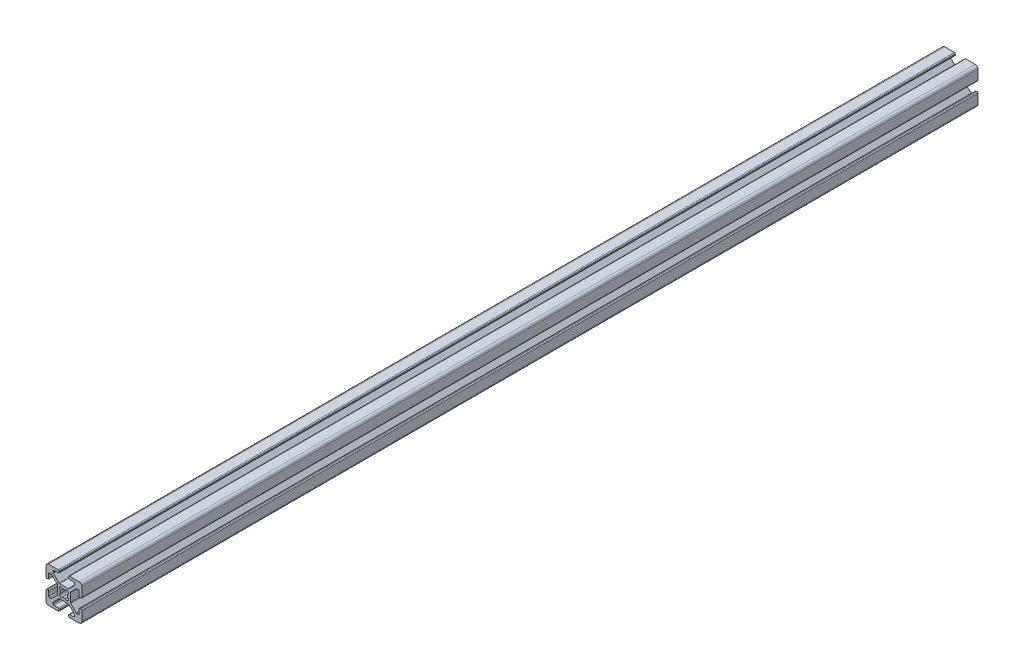
SolidWorks part; units mm, degrees
ref_plane "Front Plane" through (0, 0, 0) normal (0, 0, 1) x (1, 0, 0)
ref_plane "Top Plane" through (0, 0, 0) normal (0, 1, 0) x (1, 0, 0)
ref_plane "Right Plane" through (0, 0, 0) normal (1, 0, 0) x (0, 0, -1)
sketch "Sketch1" plane through (0, 0, 0) normal (0, 0, 1) x (1, 0, 0)
  line L0 (-5.0323, -0.3411) -> (-5.5163, -0.3411)
  line L1 (-6.0243, 0.1669) -> (-6.0243, 2.5159)
  line L2 (-4.5243, 0.1669) -> (-4.5243, 5.5289)
  line L3 (-10.8693, -5.355) -> (-10.8693, -0.5871)
  line L4 (-7.2582, 3.0239) -> (-6.5323, 3.0239)
  line L5 (-7.6174, 2.8752) -> (-10.7205, -0.2279)
  line L6 (-5.0323, -5.6011) -> (-5.5163, -5.6011)
  line L7 (-4.5243, -6.1091) -> (-4.5243, -11.4711)
  line L8 (-6.0243, -6.1091) -> (-6.0243, -8.4581)
  line L9 (-7.2582, -8.9661) -> (-6.5323, -8.9661)
  line L10 (-7.6174, -8.8173) -> (-10.7205, -5.7142)
  line L11 (-12.3994, -5.2756) -> (-12.2198, -5.096)
  line L12 (-17.1543, 6.5209) -> (-17.1543, 6.0369)
  line L13 (-17.6623, 7.0289) -> (-23.0243, 7.0289)
  line L14 (-17.6623, 5.5289) -> (-20.0113, 5.5289)
  line L15 (-12.1404, 0.6839) -> (-16.9082, 0.6839)
  line L16 (-20.5193, 4.295) -> (-20.5193, 5.0209)
  line L17 (-20.3705, 3.9358) -> (-17.2674, 0.8327)
  line L18 (-11.8943, 6.5209) -> (-11.8943, 6.0369)
  line L19 (-11.3863, 7.0289) -> (-6.0243, 7.0289)
  line L20 (-11.3863, 5.5289) -> (-9.0373, 5.5289)
  line L21 (-8.5293, 4.295) -> (-8.5293, 5.0209)
  line L22 (-8.6781, 3.9358) -> (-11.7812, 0.8327)
  line L23 (-12.2198, -0.8462) -> (-12.3994, -0.6666)
  line L24 (-24.0163, -5.6011) -> (-23.5323, -5.6011)
  line L25 (-24.5243, -6.1091) -> (-24.5243, -11.4711)
  line L26 (-23.0243, -6.1091) -> (-23.0243, -8.4581)
  line L27 (-18.1793, -0.5871) -> (-18.1793, -5.355)
  line L28 (-21.7904, -8.9661) -> (-22.5163, -8.9661)
  line L29 (-21.4312, -8.8173) -> (-18.3281, -5.7142)
  line L30 (-24.0163, -0.3411) -> (-23.5323, -0.3411)
  line L31 (-24.5243, 0.1669) -> (-24.5243, 5.5289)
  line L32 (-23.0243, 0.1669) -> (-23.0243, 2.5159)
  line L33 (-21.7904, 3.0239) -> (-22.5163, 3.0239)
  line L34 (-21.4312, 2.8752) -> (-18.3281, -0.2279)
  line L35 (-16.6492, -0.6666) -> (-16.8288, -0.8462)
  line L36 (-11.8943, -12.4631) -> (-11.8943, -11.9791)
  line L37 (-11.3863, -12.9711) -> (-6.0243, -12.9711)
  line L38 (-11.3863, -11.4711) -> (-9.0373, -11.4711)
  line L39 (-16.9082, -6.6261) -> (-12.1404, -6.6261)
  line L40 (-8.5293, -10.2371) -> (-8.5293, -10.9631)
  line L41 (-8.6781, -9.8779) -> (-11.7812, -6.7748)
  line L42 (-17.1543, -12.4631) -> (-17.1543, -11.9791)
  line L43 (-17.6623, -12.9711) -> (-23.0243, -12.9711)
  line L44 (-17.6623, -11.4711) -> (-20.0113, -11.4711)
  line L45 (-20.5193, -10.2371) -> (-20.5193, -10.9631)
  line L46 (-20.3705, -9.8779) -> (-17.2674, -6.7748)
  line L47 (-16.8288, -5.096) -> (-16.6492, -5.2756)
  arc A0 (-15.3283, -4.9062) -> (-13.7203, -4.9062) centre (-14.5243, -2.9711) ccw
  arc A1 (-6.0243, 2.5159) -> (-6.5323, 3.0239) centre (-6.5323, 2.5159) ccw
  arc A2 (-7.2582, 3.0239) -> (-7.6174, 2.8752) centre (-7.2582, 2.5159) ccw
  arc A3 (-10.7205, -0.2279) -> (-10.8693, -0.5871) centre (-10.3613, -0.5871) ccw
  arc A4 (-10.8693, -5.355) -> (-10.7205, -5.7142) centre (-10.3613, -5.355) ccw
  arc A5 (-7.6174, -8.8173) -> (-7.2582, -8.9661) centre (-7.2582, -8.4581) ccw
  arc A6 (-6.5323, -8.9661) -> (-6.0243, -8.4581) centre (-6.5323, -8.4581) ccw
  arc A7 (-5.5163, -5.6011) -> (-6.0243, -6.1091) centre (-5.5163, -6.1091) ccw
  arc A8 (-4.5243, -6.1091) -> (-5.0323, -5.6011) centre (-5.0323, -6.1091) ccw
  arc A9 (-5.0323, -0.3411) -> (-4.5243, 0.1669) centre (-5.0323, 0.1669) ccw
  arc A10 (-6.0243, 0.1669) -> (-5.5163, -0.3411) centre (-5.5163, 0.1669) ccw
  arc A11 (-13.7203, -4.9062) -> (-12.3994, -5.2756) centre (-12.9559, -4.7191) ccw
  arc A12 (-12.2198, -5.096) -> (-12.5892, -3.775) centre (-12.7763, -4.5395) ccw
  arc A13 (-17.1543, 6.5209) -> (-17.6623, 7.0289) centre (-17.6623, 6.5209) ccw
  arc A14 (-17.6623, 5.5289) -> (-17.1543, 6.0369) centre (-17.6623, 6.0369) ccw
  arc A15 (-12.5892, -3.775) -> (-12.5892, -2.1671) centre (-14.5243, -2.9711) ccw
  arc A16 (-17.2674, 0.8327) -> (-16.9082, 0.6839) centre (-16.9082, 1.1919) ccw
  arc A17 (-20.0113, 5.5289) -> (-20.5193, 5.0209) centre (-20.0113, 5.0209) ccw
  arc A18 (-20.5193, 4.295) -> (-20.3705, 3.9358) centre (-20.0113, 4.295) ccw
  arc A19 (-11.8943, 6.0369) -> (-11.3863, 5.5289) centre (-11.3863, 6.0369) ccw
  arc A20 (-11.3863, 7.0289) -> (-11.8943, 6.5209) centre (-11.3863, 6.5209) ccw
  arc A21 (-8.5293, 5.0209) -> (-9.0373, 5.5289) centre (-9.0373, 5.0209) ccw
  arc A22 (-8.6781, 3.9358) -> (-8.5293, 4.295) centre (-9.0373, 4.295) ccw
  arc A23 (-12.1404, 0.6839) -> (-11.7812, 0.8327) centre (-12.1404, 1.1919) ccw
  arc A24 (-12.5892, -2.1671) -> (-12.2198, -0.8462) centre (-12.7763, -1.4027) ccw
  arc A25 (-12.3994, -0.6666) -> (-13.7203, -1.0359) centre (-12.9559, -1.223) ccw
  arc A26 (-24.0163, -5.6011) -> (-24.5243, -6.1091) centre (-24.0163, -6.1091) ccw
  arc A27 (-23.0243, -6.1091) -> (-23.5323, -5.6011) centre (-23.5323, -6.1091) ccw
  arc A28 (-13.7203, -1.0359) -> (-15.3283, -1.0359) centre (-14.5243, -2.9711) ccw
  arc A29 (-18.3281, -5.7142) -> (-18.1793, -5.355) centre (-18.6873, -5.355) ccw
  arc A30 (-23.0243, -8.4581) -> (-22.5163, -8.9661) centre (-22.5163, -8.4581) ccw
  arc A31 (-21.7904, -8.9661) -> (-21.4312, -8.8173) centre (-21.7904, -8.4581) ccw
  arc A32 (-23.5323, -0.3411) -> (-23.0243, 0.1669) centre (-23.5323, 0.1669) ccw
  arc A33 (-24.5243, 0.1669) -> (-24.0163, -0.3411) centre (-24.0163, 0.1669) ccw
  arc A34 (-22.5163, 3.0239) -> (-23.0243, 2.5159) centre (-22.5163, 2.5159) ccw
  arc A35 (-21.4312, 2.8752) -> (-21.7904, 3.0239) centre (-21.7904, 2.5159) ccw
  arc A36 (-18.1793, -0.5871) -> (-18.3281, -0.2279) centre (-18.6873, -0.5871) ccw
  arc A37 (-15.3283, -1.0359) -> (-16.6492, -0.6666) centre (-16.0927, -1.223) ccw
  arc A38 (-16.8288, -0.8462) -> (-16.4594, -2.1671) centre (-16.2723, -1.4027) ccw
  arc A39 (-11.8943, -12.4631) -> (-11.3863, -12.9711) centre (-11.3863, -12.4631) ccw
  arc A40 (-11.3863, -11.4711) -> (-11.8943, -11.9791) centre (-11.3863, -11.9791) ccw
  arc A41 (-16.4594, -2.1671) -> (-16.4594, -3.775) centre (-14.5243, -2.9711) ccw
  arc A42 (-11.7812, -6.7748) -> (-12.1404, -6.6261) centre (-12.1404, -7.1341) ccw
  arc A43 (-9.0373, -11.4711) -> (-8.5293, -10.9631) centre (-9.0373, -10.9631) ccw
  arc A44 (-8.5293, -10.2371) -> (-8.6781, -9.8779) centre (-9.0373, -10.2371) ccw
  arc A45 (-17.1543, -11.9791) -> (-17.6623, -11.4711) centre (-17.6623, -11.9791) ccw
  arc A46 (-17.6623, -12.9711) -> (-17.1543, -12.4631) centre (-17.6623, -12.4631) ccw
  arc A47 (-20.5193, -10.9631) -> (-20.0113, -11.4711) centre (-20.0113, -10.9631) ccw
  arc A48 (-20.3705, -9.8779) -> (-20.5193, -10.2371) centre (-20.0113, -10.2371) ccw
  arc A49 (-16.9082, -6.6261) -> (-17.2674, -6.7748) centre (-16.9082, -7.1341) ccw
  arc A50 (-16.4594, -3.775) -> (-16.8288, -5.096) centre (-16.2723, -4.5395) ccw
  arc A51 (-16.6492, -5.2756) -> (-15.3283, -4.9062) centre (-16.0927, -4.7191) ccw
  arc A52 (-4.5243, 5.5289) -> (-6.0243, 7.0289) centre (-6.0243, 5.5289) ccw
  arc A53 (-6.0243, -12.9711) -> (-4.5243, -11.4711) centre (-6.0243, -11.4711) ccw
  arc A54 (-24.5243, -11.4711) -> (-23.0243, -12.9711) centre (-23.0243, -11.4711) ccw
  arc A55 (-23.0243, 7.0289) -> (-24.5243, 5.5289) centre (-23.0243, 5.5289) ccw
extrude "Extrude1" add sketch "Sketch1" along normal blind 500
